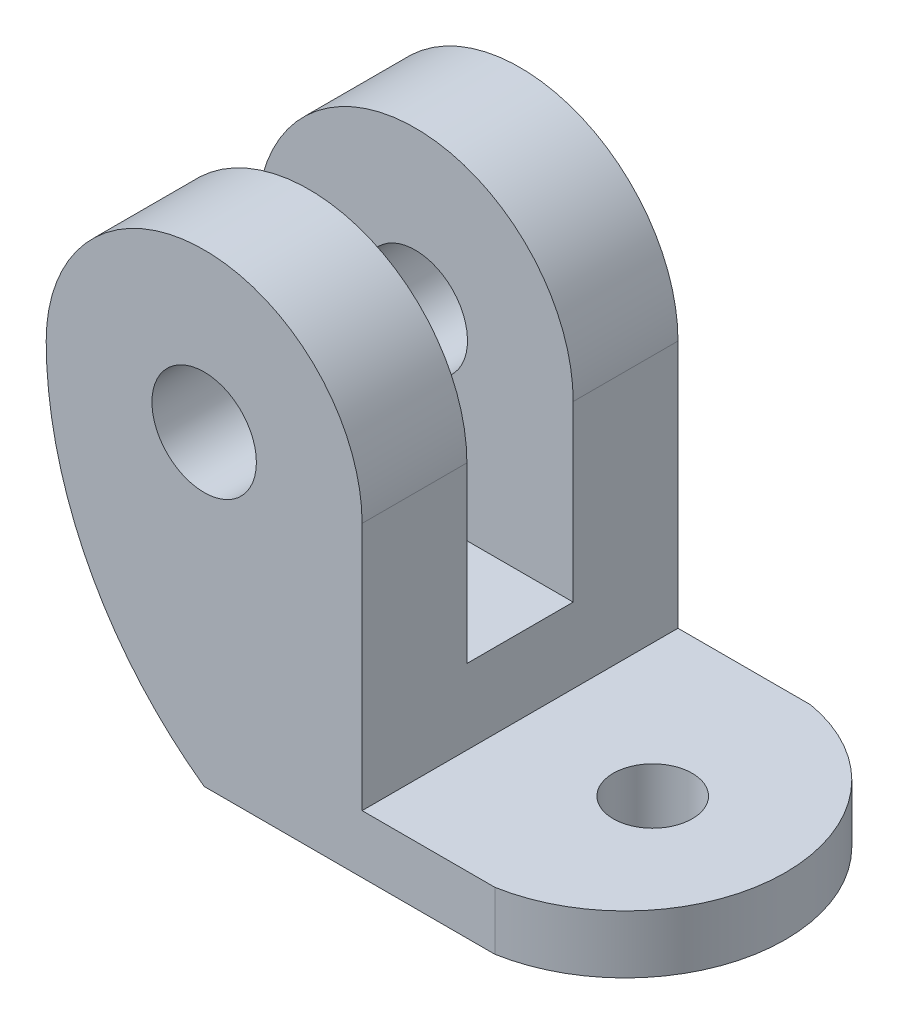
SolidWorks part; units mm, degrees
material "ABS"
ref_plane "Front Plane" through (0, 0, 0) normal (0, 0, 1) x (1, 0, 0)
ref_plane "Top Plane" through (0, 0, 0) normal (0, 1, 0) x (1, 0, 0)
ref_plane "Right Plane" through (0, 0, 0) normal (1, 0, 0) x (0, 0, -1)
sketch "Sketch1" plane through (0, 0, 0) normal (0, 0, 1) x (1, 0, 0)
  line L0 (4.7625, 9.25) -> (4.7625, 1.75)
  line L1 (4.7625, 1.75) -> (12.7625, 1.75)
  line L2 (12.7625, 1.75) -> (12.7625, 0)
  line L3 (12.7625, 0) -> (0, 0)
  line L4 (4.7625, 9.25) -> (-4.7625, 9.25) construction
  line L5 (0, 9.25) -> (0, 0) construction
  arc A0 (-4.7625, 9.25) -> (4.7625, 9.25) centre (0, 9.25) cw
  circle A1 centre (0, 9.25) radius 1.575
  circle A2 centre (0, 9.25) radius 4.7625 construction
  arc A3 (-4.7625, 9.25) -> (0, 0) centre (6.6017, 9.25) ccw
  dimension "D4" = 3.15
  dimension "D1" = 7.5
  dimension "D2" = 4.7625
  dimension "D3" = 1.75
  dimension "D5" = 12.7625
extrude "Boss-Extrude1" add sketch "Sketch1" along normal blind 9.525
sketch "Sketch2" plane through (4.7625, 0, 0) normal (-1, 0, 0) x (0, 0, 1)
  line L1 (6.365, 14.0125) -> (6.365, 4.0125)
  line L2 (9.525, 14.0125) -> (0, 14.0125) construction
  line L3 (6.365, 4.0125) -> (3.16, 4.0125)
  line L4 (3.16, 4.0125) -> (3.16, 14.0125)
  line L5 (3.16, 14.0125) -> (6.365, 14.0125)
  line L6 (9.525, 9.25) -> (9.525, 14.0125) construction
  line L7 (0, 14.0125) -> (0, 9.25) construction
  dimension "D1" = 3.16
  dimension "D2" = 3.16
  dimension "D3" = 10
extrude "Cut-Extrude4" cut sketch "Sketch2" along normal up to surface (8.4789 mm away)
sketch "Sketch4" plane through (0, 1.75, 0) normal (0, 1, 0) x (1, 0, 0)
  line L0 (8.7625, 0) -> (8.7625, -9.525) construction
  line L1 (12.7625, 0) -> (4.7625, 0) construction
  line L2 (12.7625, -9.525) -> (4.7625, -9.525) construction
  line L3 (0, 0) -> (0, -9.525) construction
  line L4 (-4.7625, -9.525) -> (4.7625, -9.525) construction
  line L5 (8.7625, 0) -> (12.7625, 0)
  line L6 (12.7625, 0) -> (12.7625, -4.7625)
  line L7 (12.7625, -9.525) -> (12.7625, 0) construction
  line L8 (12.7625, -9.525) -> (8.7625, -9.525)
  line L9 (12.7625, -4.7625) -> (12.7625, -9.525)
  line L10 (8.7625, -9.525) -> (12.7625, -9.525)
  circle A0 centre (8.7625, -4.7625) radius 1.1906
  circle A1 centre (-8.7625, -4.7625) radius 1.1906 construction
  arc A2 (8.7625, 0) -> (8.7625, -9.525) centre (7.9273, -4.7625) cw
  dimension "D1" = 2.3813
extrude "Cut-Extrude5" cut sketch "Sketch4" against normal up to surface (1.75 mm away)
